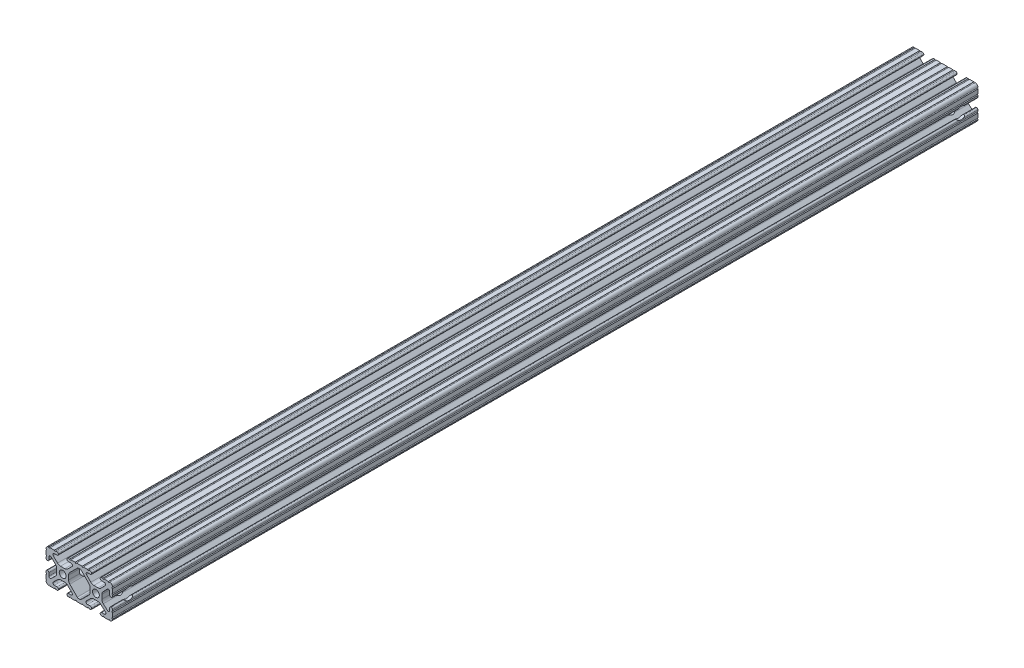
SolidWorks part; units mm, degrees
ref_plane "Front Plane" through (0, 0, 0) normal (0, 0, 1) x (1, 0, 0)
ref_plane "Top Plane" through (0, 0, 0) normal (0, 1, 0) x (1, 0, 0)
ref_plane "Right Plane" through (0, 0, 0) normal (1, 0, 0) x (0, 0, -1)
sketch "Sketch1" plane through (0, 0, 0) normal (0, 0, 1) x (1, 0, 0)
  line L0 (-7.2595, -3.8694) -> (-1.5457, -9.5728)
  line L1 (-8.1915, 1.6223) -> (-8.1915, -1.6223)
  line L2 (-1.504, 9.5765) -> (-7.252, 3.8768)
  line L3 (0.5515, 10.033) -> (-0.3952, 10.033)
  line L4 (7.2829, 3.8459) -> (1.6756, 9.5611)
  line L5 (8.1915, -1.6223) -> (8.1915, 1.6223)
  line L6 (1.5457, -9.5728) -> (7.2595, -3.8694)
  line L7 (-0.4332, -10.033) -> (0.4332, -10.033)
  line L8 (18.0171, 12.7) -> (16.9875, 12.7)
  line L9 (15.9385, 11.651) -> (15.9385, 11.5392)
  line L10 (16.9875, 10.4902) -> (19.1164, 10.4902)
  line L11 (19.8441, 8.7652) -> (16.619, 5.4551)
  line L12 (14.3449, 4.4958) -> (11.0833, 4.4958)
  line L13 (8.817, 5.4472) -> (5.5642, 8.7627)
  line L14 (6.2894, 10.4902) -> (8.4125, 10.4902)
  line L15 (9.4615, 11.5392) -> (9.4615, 11.651)
  line L16 (8.4125, 12.7) -> (7.3829, 12.7)
  line L17 (6.3669, 12.7) -> (3.1496, 12.7)
  line L18 (2.1336, 12.7) -> (-2.1336, 12.7)
  line L19 (-3.1496, 12.7) -> (-6.3669, 12.7)
  line L20 (-7.3829, 12.7) -> (-8.4125, 12.7)
  line L21 (-9.4615, 11.651) -> (-9.4615, 11.5392)
  line L22 (-8.4125, 10.4902) -> (-6.2836, 10.4902)
  line L23 (-5.5326, 8.6661) -> (-8.81, 5.4163)
  line L24 (-11.0455, 4.4958) -> (-14.3545, 4.4958)
  line L25 (-16.59, 5.4163) -> (-19.8674, 8.6661)
  line L26 (-19.1164, 10.4902) -> (-16.9875, 10.4902)
  line L27 (-15.9385, 11.5392) -> (-15.9385, 11.651)
  line L28 (-16.9875, 12.7) -> (-18.0171, 12.7)
  line L29 (-19.0331, 12.7) -> (-22.2504, 12.7)
  line L30 (-25.4, 9.5504) -> (-25.4, 6.3331)
  line L31 (-25.4, 5.3171) -> (-25.4, 4.2375)
  line L32 (-24.401, 3.2385) -> (-24.2392, 3.2385)
  line L33 (-23.1902, 4.2875) -> (-23.1902, 6.3347)
  line L34 (-21.434, 7.0665) -> (-18.148, 3.8082)
  line L35 (-17.2085, 1.5536) -> (-17.2085, -1.6952)
  line L36 (-18.1405, -3.9423) -> (-21.4316, -7.2274)
  line L37 (-23.1902, -6.498) -> (-23.1902, -4.2875)
  line L38 (-24.2392, -3.2385) -> (-24.351, -3.2385)
  line L39 (-25.4, -4.2875) -> (-25.4, -5.3171)
  line L40 (-25.4, -6.3331) -> (-25.4, -9.5504)
  line L41 (-22.2504, -12.7) -> (-19.0331, -12.7)
  line L42 (-18.0171, -12.7) -> (-16.9875, -12.7)
  line L43 (-15.9384, -11.651) -> (-15.9384, -11.5392)
  line L44 (-16.9875, -10.4902) -> (-19.1164, -10.4902)
  line L45 (-19.8341, -8.7551) -> (-16.4966, -5.4237)
  line L46 (-14.2536, -4.4958) -> (-11.1464, -4.4958)
  line L47 (-8.9034, -5.4237) -> (-5.5659, -8.7551)
  line L48 (-6.2836, -10.4902) -> (-8.4125, -10.4902)
  line L49 (-9.4616, -11.5392) -> (-9.4616, -11.651)
  line L50 (-8.4125, -12.7) -> (-7.3829, -12.7)
  line L51 (-6.3669, -12.7) -> (-3.1496, -12.7)
  line L52 (-2.1336, -12.7) -> (2.1336, -12.7)
  line L53 (3.1496, -12.7) -> (6.3669, -12.7)
  line L54 (7.3829, -12.7) -> (8.4125, -12.7)
  line L55 (9.4616, -11.651) -> (9.4616, -11.5392)
  line L56 (8.4125, -10.4902) -> (6.2894, -10.4902)
  line L57 (5.4807, -8.5353) -> (8.5979, -5.4237)
  line L58 (10.8409, -4.4958) -> (14.1026, -4.4958)
  line L59 (16.1879, -5.2766) -> (19.8682, -8.4822)
  line L60 (19.1164, -10.4902) -> (16.9875, -10.4902)
  line L61 (15.9384, -11.5392) -> (15.9384, -11.651)
  line L62 (16.9875, -12.7) -> (18.0171, -12.7)
  line L63 (19.0331, -12.7) -> (22.2504, -12.7)
  line L64 (25.4, -9.5504) -> (25.4, -6.3331)
  line L65 (25.4, -5.3171) -> (25.4, -4.2375)
  line L66 (24.401, -3.2385) -> (24.1892, -3.2385)
  line L67 (23.1902, -4.2375) -> (23.1902, -6.1559)
  line L68 (21.584, -6.8869) -> (18.2982, -4.025)
  line L69 (17.2085, -1.6308) -> (17.2085, 1.6308)
  line L70 (18.1094, 3.8465) -> (21.5263, 7.3534)
  line L71 (23.1902, 6.6769) -> (23.1902, 4.2375)
  line L72 (24.1892, 3.2385) -> (24.401, 3.2385)
  line L73 (25.4, 4.2375) -> (25.4, 5.3171)
  line L74 (25.4, 6.3332) -> (25.4, 9.5504)
  line L75 (22.2504, 12.7) -> (19.0331, 12.7)
  circle A0 centre (-12.7, 0) radius 2.6035
  circle A1 centre (12.7, 0) radius 2.6035
  arc A2 (-1.5457, -9.5728) -> (-0.4332, -10.033) centre (-0.4332, -8.4582) ccw
  arc A3 (-8.1915, -1.6223) -> (-7.2595, -3.8694) centre (-5.0165, -1.6223) ccw
  arc A4 (-7.252, 3.8768) -> (-8.1915, 1.6223) centre (-5.0165, 1.6223) ccw
  arc A5 (-0.3952, 10.033) -> (-1.504, 9.5765) centre (-0.3952, 8.4582) ccw
  arc A6 (1.6756, 9.5611) -> (0.5515, 10.033) centre (0.5515, 8.4582) ccw
  arc A7 (8.1915, 1.6223) -> (7.2829, 3.8459) centre (5.0165, 1.6223) ccw
  arc A8 (7.2595, -3.8694) -> (8.1915, -1.6223) centre (5.0165, -1.6223) ccw
  arc A9 (0.4332, -10.033) -> (1.5457, -9.5728) centre (0.4332, -8.4582) ccw
  arc A10 (18.0171, 12.7) -> (19.0331, 12.7) centre (18.5251, 12.7) ccw
  arc A11 (16.9875, 12.7) -> (15.9385, 11.651) centre (16.9875, 11.651) ccw
  arc A12 (15.9385, 11.5392) -> (16.9875, 10.4902) centre (16.9875, 11.5392) ccw
  arc A13 (19.8441, 8.7652) -> (19.1164, 10.4902) centre (19.1164, 9.4742) ccw
  arc A14 (14.3449, 4.4958) -> (16.619, 5.4551) centre (14.3449, 7.6708) ccw
  arc A15 (8.817, 5.4472) -> (11.0833, 4.4958) centre (11.0833, 7.6708) ccw
  arc A16 (6.2894, 10.4902) -> (5.5642, 8.7627) centre (6.2894, 9.4742) ccw
  arc A17 (8.4125, 10.4902) -> (9.4615, 11.5392) centre (8.4125, 11.5392) ccw
  arc A18 (9.4615, 11.651) -> (8.4125, 12.7) centre (8.4125, 11.651) ccw
  arc A19 (6.3669, 12.7) -> (7.3829, 12.7) centre (6.8749, 12.7) ccw
  arc A20 (2.1336, 12.7) -> (3.1496, 12.7) centre (2.6416, 12.7) ccw
  arc A21 (-3.1496, 12.7) -> (-2.1336, 12.7) centre (-2.6416, 12.7) ccw
  arc A22 (-7.3829, 12.7) -> (-6.3669, 12.7) centre (-6.8749, 12.7) ccw
  arc A23 (-8.4125, 12.7) -> (-9.4615, 11.651) centre (-8.4125, 11.651) ccw
  arc A24 (-9.4615, 11.5392) -> (-8.4125, 10.4902) centre (-8.4125, 11.5392) ccw
  arc A25 (-5.5326, 8.6661) -> (-6.2836, 10.4902) centre (-6.2836, 9.4235) ccw
  arc A26 (-11.0455, 4.4958) -> (-8.81, 5.4163) centre (-11.0455, 7.6708) ccw
  arc A27 (-16.59, 5.4163) -> (-14.3545, 4.4958) centre (-14.3545, 7.6708) ccw
  arc A28 (-19.1164, 10.4902) -> (-19.8674, 8.6661) centre (-19.1164, 9.4235) ccw
  arc A29 (-16.9875, 10.4902) -> (-15.9385, 11.5392) centre (-16.9875, 11.5392) ccw
  arc A30 (-15.9385, 11.651) -> (-16.9875, 12.7) centre (-16.9875, 11.651) ccw
  arc A31 (-19.0331, 12.7) -> (-18.0171, 12.7) centre (-18.5251, 12.7) ccw
  arc A32 (-23.2664, 12.6998) -> (-22.2504, 12.7) centre (-22.7584, 12.7) ccw
  arc A33 (-23.2664, 12.6998) -> (-25.3998, 10.5664) centre (-23.2918, 10.5918) ccw
  arc A34 (-25.4, 9.5504) -> (-25.3998, 10.5664) centre (-25.4, 10.0584) ccw
  arc A35 (-25.4, 5.3171) -> (-25.4, 6.3331) centre (-25.4, 5.8251) ccw
  arc A36 (-25.4, 4.2375) -> (-24.401, 3.2385) centre (-24.401, 4.2375) ccw
  arc A37 (-24.2392, 3.2385) -> (-23.1902, 4.2875) centre (-24.2392, 4.2875) ccw
  arc A38 (-21.434, 7.0665) -> (-23.1902, 6.3347) centre (-22.1596, 6.3347) ccw
  arc A39 (-17.2085, 1.5536) -> (-18.148, 3.8082) centre (-20.3835, 1.5536) ccw
  arc A40 (-18.1405, -3.9423) -> (-17.2085, -1.6952) centre (-20.3835, -1.6952) ccw
  arc A41 (-23.1902, -6.498) -> (-21.4316, -7.2274) centre (-22.1596, -6.498) ccw
  arc A42 (-23.1902, -4.2875) -> (-24.2392, -3.2385) centre (-24.2392, -4.2875) ccw
  arc A43 (-24.351, -3.2385) -> (-25.4, -4.2875) centre (-24.351, -4.2875) ccw
  arc A44 (-25.4, -6.3331) -> (-25.4, -5.3171) centre (-25.4, -5.8251) ccw
  arc A45 (-25.3998, -10.5664) -> (-25.4, -9.5504) centre (-25.4, -10.0584) ccw
  arc A46 (-25.3998, -10.5664) -> (-23.2664, -12.6998) centre (-23.2918, -10.5918) ccw
  arc A47 (-22.2504, -12.7) -> (-23.2664, -12.6998) centre (-22.7584, -12.7) ccw
  arc A48 (-18.0171, -12.7) -> (-19.0331, -12.7) centre (-18.5251, -12.7) ccw
  arc A49 (-16.9875, -12.7) -> (-15.9384, -11.651) centre (-16.9875, -11.651) ccw
  arc A50 (-15.9384, -11.5392) -> (-16.9875, -10.4902) centre (-16.9875, -11.5392) ccw
  arc A51 (-19.8341, -8.7551) -> (-19.1164, -10.4902) centre (-19.1164, -9.4742) ccw
  arc A52 (-14.2536, -4.4958) -> (-16.4966, -5.4237) centre (-14.2536, -7.6708) ccw
  arc A53 (-8.9034, -5.4237) -> (-11.1464, -4.4958) centre (-11.1464, -7.6708) ccw
  arc A54 (-6.2836, -10.4902) -> (-5.5659, -8.7551) centre (-6.2836, -9.4742) ccw
  arc A55 (-8.4125, -10.4902) -> (-9.4616, -11.5392) centre (-8.4125, -11.5392) ccw
  arc A56 (-9.4616, -11.651) -> (-8.4125, -12.7) centre (-8.4125, -11.651) ccw
  arc A57 (-6.3669, -12.7) -> (-7.3829, -12.7) centre (-6.8749, -12.7) ccw
  arc A58 (-2.1336, -12.7) -> (-3.1496, -12.7) centre (-2.6416, -12.7) ccw
  arc A59 (3.1496, -12.7) -> (2.1336, -12.7) centre (2.6416, -12.7) ccw
  arc A60 (7.3829, -12.7) -> (6.3669, -12.7) centre (6.8749, -12.7) ccw
  arc A61 (8.4125, -12.7) -> (9.4616, -11.651) centre (8.4125, -11.651) ccw
  arc A62 (9.4616, -11.5392) -> (8.4125, -10.4902) centre (8.4125, -11.5392) ccw
  arc A63 (5.4807, -8.5353) -> (6.2894, -10.4902) centre (6.2894, -9.3455) ccw
  arc A64 (10.8409, -4.4958) -> (8.5979, -5.4237) centre (10.8409, -7.6708) ccw
  arc A65 (16.1879, -5.2766) -> (14.1026, -4.4958) centre (14.1026, -7.6708) ccw
  arc A66 (19.1164, -10.4902) -> (19.8682, -8.4822) centre (19.1164, -9.3455) ccw
  arc A67 (16.9875, -10.4902) -> (15.9384, -11.5392) centre (16.9875, -11.5392) ccw
  arc A68 (15.9384, -11.651) -> (16.9875, -12.7) centre (16.9875, -11.651) ccw
  arc A69 (19.0331, -12.7) -> (18.0171, -12.7) centre (18.5251, -12.7) ccw
  arc A70 (23.2664, -12.6998) -> (22.2504, -12.7) centre (22.7584, -12.7) ccw
  arc A71 (23.2664, -12.6998) -> (25.3998, -10.5664) centre (23.2918, -10.5918) ccw
  arc A72 (25.4, -9.5504) -> (25.3998, -10.5664) centre (25.4, -10.0584) ccw
  arc A73 (25.4, -5.3171) -> (25.4, -6.3331) centre (25.4, -5.8251) ccw
  arc A74 (25.4, -4.2375) -> (24.401, -3.2385) centre (24.401, -4.2375) ccw
  arc A75 (24.1892, -3.2385) -> (23.1902, -4.2375) centre (24.1892, -4.2375) ccw
  arc A76 (21.584, -6.8869) -> (23.1902, -6.1559) centre (22.2207, -6.1559) ccw
  arc A77 (17.2085, -1.6308) -> (18.2982, -4.025) centre (20.3835, -1.6308) ccw
  arc A78 (18.1094, 3.8465) -> (17.2085, 1.6308) centre (20.3835, 1.6308) ccw
  arc A79 (23.1902, 6.6769) -> (21.5263, 7.3534) centre (22.2207, 6.6769) ccw
  arc A80 (23.1902, 4.2375) -> (24.1892, 3.2385) centre (24.1892, 4.2375) ccw
  arc A81 (24.401, 3.2385) -> (25.4, 4.2375) centre (24.401, 4.2375) ccw
  arc A82 (25.4, 6.3332) -> (25.4, 5.3171) centre (25.4, 5.8251) ccw
  arc A83 (25.3998, 10.5664) -> (25.4, 9.5504) centre (25.4, 10.0584) ccw
  arc A84 (25.3998, 10.5664) -> (23.2664, 12.6998) centre (23.2918, 10.5918) ccw
  arc A85 (22.2504, 12.7) -> (23.2664, 12.6998) centre (22.7584, 12.7) ccw
  point P248 (0, 10.033)
extrude "Boss-Extrude1" add sketch "Sketch1" along normal mid plane 660.4
sketch "Sketch2" plane through (-17.2085, 0, 0) normal (-1, 0, 0) x (0, 0, 1)
  line L0 (0, 1.5536) -> (0, 82.0272) construction
  line L1 (330.2, 1.5536) -> (-330.2, 1.5536) construction
  circle A0 centre (-317.5, 0) radius 4.445
  circle A1 centre (317.5, 0) radius 4.445
  dimension "D1" = 8.89
  dimension "D2" = 317.5
extrude "Cut-Extrude1" cut sketch "Sketch2" against normal through all both and the other way through all
